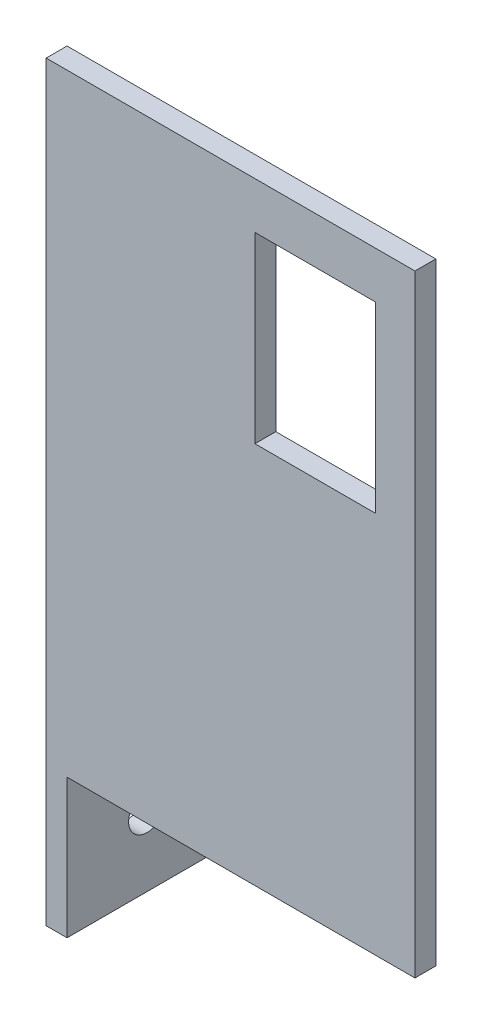
SolidWorks part; units mm, degrees
ref_plane "前视基准面" through (0, 0, 0) normal (0, 0, 1) x (1, 0, 0)
ref_plane "上视基准面" through (0, 0, 0) normal (0, 1, 0) x (1, 0, 0)
ref_plane "右视基准面" through (0, 0, 0) normal (1, 0, 0) x (0, 0, -1)
sketch "草图1" plane through (0, 0, 0) normal (0, 1, 0) x (1, 0, 0)
  line L1 (-14.6364, 11.377) -> (8.3636, 11.377)
  line L2 (-14.6364, 11.377) -> (-14.6364, -11.623)
  line L3 (-14.6364, -11.623) -> (8.3636, -11.623)
  line L4 (8.3636, 11.377) -> (8.3636, -11.623)
  dimension "D1" = 23
  dimension "D2" = 23
extrude "凸台-拉伸1" add sketch "草图1" along normal blind 3
sketch "草图3" plane through (0, 3, 0) normal (0, 1, 0) x (1, 0, 0)
  line L0 (8.3636, -11.623) -> (8.3636, 11.377) construction
  circle A0 centre (-1.6364, -0.123) radius 2.65
  dimension "D1" = 5.3
  dimension "D2" = 10
extrude "切除-拉伸1" cut sketch "草图3" against normal blind 3
sketch "草图4" plane through (0, 0, 0) normal (0, -1, 0) x (1, 0, 0)
  line L0 (-14.6364, 11.623) -> (8.3636, 11.623) construction
  line L1 (-14.6364, -11.377) -> (-11.6364, -11.377)
  line L2 (-14.6364, -11.377) -> (-14.6364, 11.623)
  line L3 (-14.6364, 11.623) -> (-11.6364, 11.623)
  line L4 (-11.6364, -11.377) -> (-11.6364, 11.623)
  dimension "D1" = 3
extrude "凸台-拉伸2" add sketch "草图4" along normal blind 20
sketch "草图5" plane through (-11.6364, 0, 0) normal (1, 0, 0) x (0, 0, -1)
  circle A0 centre (-0.123, -10) radius 2.65
  dimension "D1" = 5.3
extrude "切除-拉伸2" cut sketch "草图5" against normal blind 20
sketch "草图6" plane through (0, 3, 0) normal (0, 1, 0) x (1, 0, 0)
  line L0 (8.3636, -11.623) -> (8.3636, 11.377) construction
  line L1 (-14.6364, -11.623) -> (8.3636, -11.623)
  line L2 (-14.6364, -11.623) -> (-14.6364, -8.623)
  line L3 (-14.6364, -8.623) -> (8.3636, -8.623)
  line L4 (8.3636, -11.623) -> (8.3636, -8.623)
  dimension "D1" = 3
extrude "凸台-拉伸3" add sketch "草图6" along normal blind 85
sketch "草图7" plane through (8.3636, 0, 0) normal (1, 0, 0) x (0, 0, -1)
  line L1 (-8.623, 88) -> (-11.623, 88)
  line L2 (-8.623, 88) -> (-8.623, 0)
  line L3 (-8.623, 0) -> (-11.623, 0)
  line L4 (-11.623, 88) -> (-11.623, 0)
extrude "凸台-拉伸4" add sketch "草图7" along normal blind 30
sketch "草图8" plane through (0, 0, 8.623) normal (0, 0, -1) x (-1, 0, 0)
  line L0 (14.6364, 88) -> (14.6364, 3) construction
  line L1 (-15.3636, 81.3) -> (-32.6636, 81.3)
  line L2 (-15.3636, 81.3) -> (-15.3636, 55)
  line L3 (-15.3636, 55) -> (-32.6636, 55)
  line L4 (-32.6636, 81.3) -> (-32.6636, 55)
  line L5 (-38.3636, 0) -> (-8.3636, 0) construction
  dimension "D1" = 30
  dimension "D2" = 55
  dimension "D3" = 17.3
  dimension "D4" = 26.3
extrude "切除-拉伸3" cut sketch "草图8" against normal blind 20
